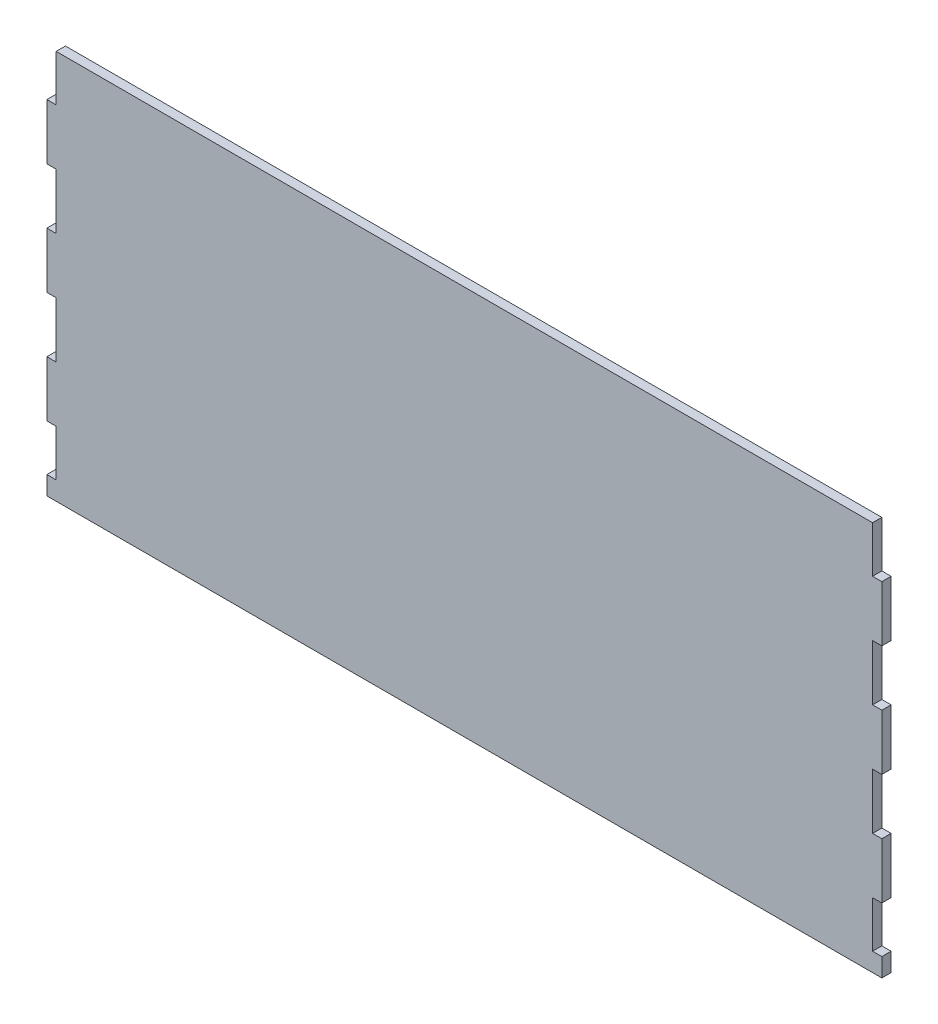
SolidWorks part; units mm, degrees
ref_plane "Front Plane" through (0, 0, 0) normal (0, 0, 1) x (1, 0, 0)
ref_plane "Top Plane" through (0, 0, 0) normal (0, 1, 0) x (1, 0, 0)
ref_plane "Right Plane" through (0, 0, 0) normal (1, 0, 0) x (0, 0, -1)
sketch "Sketch1" plane through (0, 0, 0) normal (0, 0, 1) x (1, 0, 0)
  line L1 (-225, 105) -> (225, 105)
  line L2 (-225, 105) -> (-225, -105)
  line L3 (-225, -105) -> (225, -105)
  line L4 (225, 105) -> (225, -105)
  line L5 (-225, 105) -> (225, -105) construction
  line L6 (-225, -105) -> (225, 105) construction
  point P0 (0, 0)
  dimension "D1" = 450
  dimension "D2" = 210
extrude "Boss-Extrude1" add sketch "Sketch1" along normal blind 5
sketch "Sketch3" plane through (0, 0, 0) normal (0, 0, -1) x (-1, 0, 0)
  line L0 (-225, 105) -> (225, 105) construction
  line L1 (-285.8214, 105) -> (-220, 105)
  line L2 (-285.8214, 105) -> (-285.8214, 80)
  line L3 (-285.8214, 80) -> (-220, 80)
  line L4 (-220, 105) -> (-220, 80)
  line L5 (-285.8214, 105) -> (-220, 80) construction
  line L6 (-285.8214, 80) -> (-220, 105) construction
  line L7 (-363.2287, 50) -> (-220, 50)
  line L8 (-363.2287, 50) -> (-363.2287, 20)
  line L9 (-363.2287, 20) -> (-220, 20)
  line L10 (-220, 50) -> (-220, 20)
  line L11 (-363.2287, 50) -> (-220, 20) construction
  line L12 (-363.2287, 20) -> (-220, 50) construction
  line L13 (-412.2059, -10) -> (-220, -10)
  line L14 (-412.2059, -10) -> (-412.2059, -40)
  line L15 (-412.2059, -40) -> (-220, -40)
  line L16 (-220, -10) -> (-220, -40)
  line L17 (-412.2059, -10) -> (-220, -40) construction
  line L18 (-412.2059, -40) -> (-220, -10) construction
  line L19 (-414.7079, -95) -> (-220, -95)
  line L20 (-414.7079, -95) -> (-414.7079, -70)
  line L21 (-414.7079, -70) -> (-220, -70)
  line L22 (-220, -95) -> (-220, -70)
  line L23 (-414.7079, -95) -> (-220, -70) construction
  line L24 (-414.7079, -70) -> (-220, -95) construction
  line L25 (-225, -105) -> (-225, 105) construction
  line L26 (225, -105) -> (-225, -105) construction
  line L27 (220, 105) -> (290.8214, 105)
  line L28 (220, 105) -> (220, 80)
  line L29 (220, 80) -> (290.8214, 80)
  line L30 (290.8214, 105) -> (290.8214, 80)
  line L31 (220, 105) -> (290.8214, 80) construction
  line L32 (220, 80) -> (290.8214, 105) construction
  line L33 (220, 50) -> (368.2287, 50)
  line L34 (220, 50) -> (220, 20)
  line L35 (220, 20) -> (368.2287, 20)
  line L36 (368.2287, 50) -> (368.2287, 20)
  line L37 (220, 50) -> (368.2287, 20) construction
  line L38 (220, 20) -> (368.2287, 50) construction
  line L39 (220, -10) -> (414.7059, -10)
  line L40 (220, -10) -> (220, -40)
  line L41 (220, -40) -> (414.7059, -40)
  line L42 (414.7059, -10) -> (414.7059, -40)
  line L43 (220, -10) -> (414.7059, -40) construction
  line L44 (220, -40) -> (414.7059, -10) construction
  line L45 (220, -95) -> (419.7079, -95)
  line L46 (220, -95) -> (220, -70)
  line L47 (220, -70) -> (419.7079, -70)
  line L48 (419.7079, -95) -> (419.7079, -70)
  line L49 (220, -95) -> (419.7079, -70) construction
  line L50 (220, -70) -> (419.7079, -95) construction
  line L51 (225, 105) -> (225, -105) construction
  point P0 (-252.9107, 92.5)
  point P5 (-291.6143, 35)
  point P10 (-316.1029, -25)
  point P15 (-317.354, -82.5)
  point P26 (255.4107, 92.5)
  point P31 (294.1143, 35)
  point P36 (317.3529, -25)
  point P41 (319.854, -82.5)
  dimension "D1" = 0
  dimension "D2" = 25
  dimension "D3" = 30
  dimension "D4" = 5
  dimension "D5" = 5
  dimension "D6" = 30
  dimension "D7" = 30
  dimension "D8" = 30
  dimension "D9" = 5
  dimension "D10" = 25
  dimension "D11" = 10
  dimension "D12" = 5
  dimension "D13" = 25
  dimension "D14" = 30
  dimension "D15" = 30
  dimension "D16" = 30
  dimension "D17" = 30
  dimension "D18" = 25
  dimension "D19" = 5
  dimension "D20" = 5
  dimension "D21" = 5
  dimension "D22" = 5
  dimension "D23" = 30
  dimension "D24" = 10
extrude "Cut-Extrude1" cut sketch "Sketch3" against normal through all
equation "\"10mmm\"=9.5"
